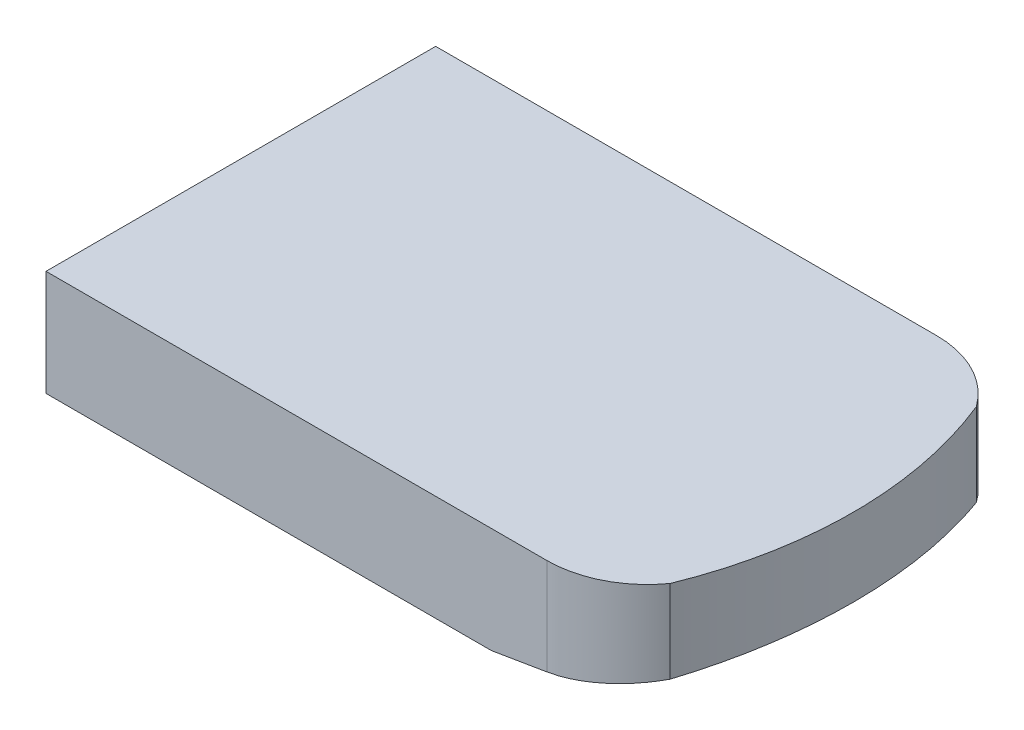
SolidWorks part; units mm, degrees
ref_plane "Front Plane" through (0, 0, 0) normal (0, 0, 1) x (1, 0, 0)
ref_plane "Top Plane" through (0, 0, 0) normal (0, 1, 0) x (1, 0, 0)
ref_plane "Right Plane" through (0, 0, 0) normal (1, 0, 0) x (0, 0, -1)
sketch "Sketch1" plane through (0, 0, 0) normal (0, 1, 0) x (1, 0, 0)
  line L1 (0, 0) -> (90, 0)
  line L2 (0, 0) -> (0, 70)
  line L3 (0, 70) -> (90, 70)
  arc A0 (104.6246, 7.5062) -> (104.6246, 62.4938) centre (37, 35) ccw
  arc A1 (104.6246, 62.4938) -> (90, 70) centre (90, 52) ccw
  arc A4 (90, 0) -> (104.6246, 7.5062) centre (90, 18) ccw
  dimension "D3" = 146
  dimension "D4" = 36
  dimension "D2" = 70
extrude "Boss-Extrude1" add sketch "Sketch1" along normal blind 19
sketch "Sketch3" plane through (0, 0, 0) normal (0, 0, 1) x (1, 0, 0)
  line L0 (110, 5) -> (80, 0)
  line L1 (110, 0) -> (80, 0)
  line L2 (110, 0) -> (110, 5)
extrude "Cut-Extrude1" cut sketch "Sketch3" against normal blind 70
